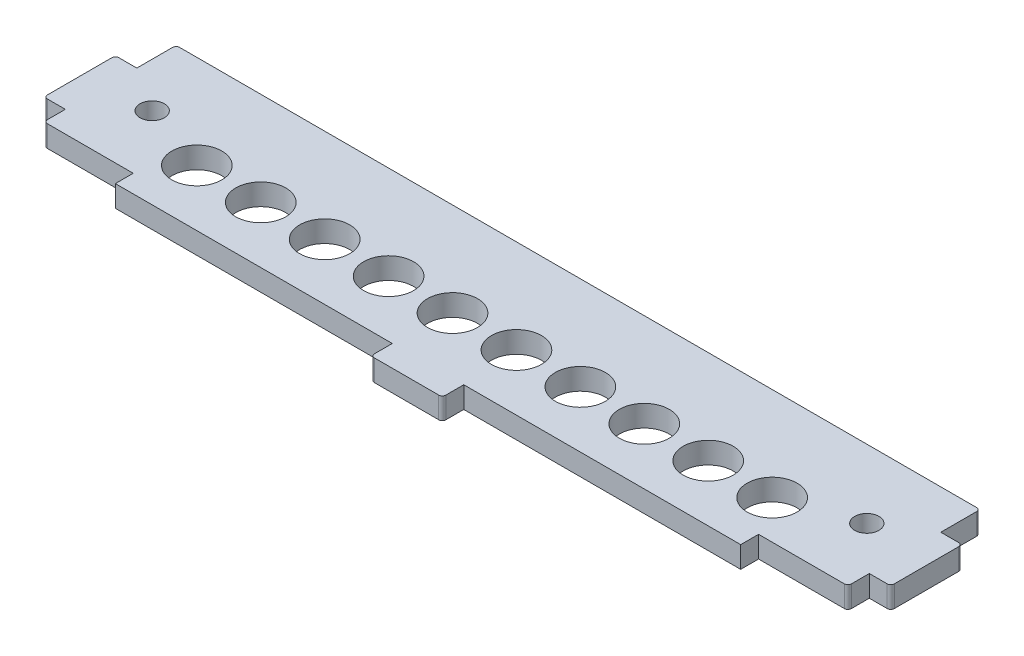
SolidWorks part; units mm, degrees
ref_plane "Спереди" through (0, 0, 0) normal (0, 0, 1) x (1, 0, 0)
ref_plane "Сверху" through (0, 0, 0) normal (0, 1, 0) x (1, 0, 0)
ref_plane "Справа" through (0, 0, 0) normal (1, 0, 0) x (0, 0, -1)
sketch "Эскиз1" plane through (0, 0, 0) normal (0, 1, 0) x (1, 0, 0)
  line L0 (0, -21) -> (0, 21.8864) construction
  line L1 (-43.75, -21) -> (43.75, -21)
  line L2 (43.75, -21) -> (43.75, -18.5)
  line L3 (43.75, -18.5) -> (56.25, -18.5)
  line L4 (56.25, -18.5) -> (56.25, -15.5)
  line L5 (56.25, -15.5) -> (59.25, -15.5)
  line L6 (59.25, -15.5) -> (59.25, -5.5)
  line L7 (59.25, -5.5) -> (56.25, -5.5)
  line L8 (56.25, -5.5) -> (56.25, 0)
  line L9 (56.25, 0) -> (-56.25, 0)
  line L10 (-56.25, -5.5) -> (-56.25, 0)
  line L11 (-59.25, -5.5) -> (-56.25, -5.5)
  line L12 (-59.25, -15.5) -> (-59.25, -5.5)
  line L13 (-56.25, -15.5) -> (-59.25, -15.5)
  line L14 (-56.25, -18.5) -> (-56.25, -15.5)
  line L15 (-43.75, -18.5) -> (-56.25, -18.5)
  line L16 (-43.75, -21) -> (-43.75, -18.5)
  line L17 (52.2732, -10.5) -> (61.8348, -10.5) construction
  line L18 (-50, -9.6) -> (-50, -5.5) construction
  line L19 (-5, -24) -> (5, -24)
  line L20 (-5, -24) -> (-5, -21)
  line L21 (-5, -21) -> (5, -21)
  line L22 (5, -24) -> (5, -21)
  line L23 (-5, -24) -> (5, -21) construction
  line L24 (-5, -21) -> (5, -24) construction
  line L25 (50, -9.6) -> (50, -6.794) construction
  circle A0 centre (-40.25, -13.1) radius 3.5
  circle A1 centre (-31.3056, -13.1) radius 3.5
  circle A2 centre (-22.3611, -13.1) radius 3.5
  circle A3 centre (-13.4167, -13.1) radius 3.5
  circle A4 centre (-4.4722, -13.1) radius 3.5
  circle A5 centre (4.4722, -13.1) radius 3.5
  circle A6 centre (13.4167, -13.1) radius 3.5
  circle A7 centre (22.3611, -13.1) radius 3.5
  circle A8 centre (31.3056, -13.1) radius 3.5
  circle A9 centre (40.25, -13.1) radius 3.5
  point P14 (50, -9.6)
  point P18 (0, 0)
  point P25 (-50, -9.6)
  point P45 (0, -22.5)
  dimension "D10" = 7
  dimension "D15" = 10
  dimension "D1" = 3
  dimension "D2" = 10
  dimension "D3" = 12.5
  dimension "D4" = 21
  dimension "D5" = 18.5
  dimension "D6" = 10.5
  dimension "D7" = 100
  dimension "D8" = 6.25
  dimension "D9" = 9.6
  dimension "D12" = 6.25
  dimension "D13" = 6.25
  dimension "D14" = 3.5
  dimension "D16" = 3
  dimension "D11" = 10
extrude "Бобышка-Вытянуть1" add sketch "Эскиз1" along normal blind 3 contours L0 L1 L2 L3 L4 L5 L6 L7 L8 L9 A9 A8 A7 A6 A5 | L1 L0 L9 L10 L11 L12 L13 L14 L15 L16 A0 A1 A2 A3 A4 | L19 L22 L1 L20
hole_wizard "Отверстие с зазором M31" positions "Эскиз2" profile "Эскиз3" hole size "M3" standard "IS"
sketch "Эскиз2" plane through (0, 3, 0) normal (0, 1, 0) x (1, 0, 0)
  point P0 (50, -9.6)
  point P2 (-50, -9.6)
sketch "Эскиз3" plane through (50, 3, 9.6) normal (1, 0, 0) x (0, 0, 1)
  line L0 (0, 0) -> (0, 11.0215)
  line L1 (0, 11.0215) -> (1.7, 10)
  line L2 (1.7, 10) -> (1.7, 0)
  line L5 (1.7, 0) -> (0, 0)
  line L10 (0, 11.0215) -> (-1.7, 10) construction
  line L11 (0, -6.35) -> (0, 107.95) construction
  dimension "Диаметр отверстия" = 3.4
  dimension "Глубина отверстия" = 10
  dimension "Угол заточки сверла" = 118
sketch "Эскиз4" plane through (0, 3, 0) normal (0, 1, 0) x (1, 0, 0)
  line L0 (-22.3611, -17.3679) -> (-20.8611, -19.966)
  line L1 (-42.25, -18.35) -> (-38.25, -18.35)
  line L2 (-42.25, -18.35) -> (-42.25, -19.85)
  line L3 (-42.25, -19.85) -> (-38.25, -19.85)
  line L4 (-38.25, -18.35) -> (-38.25, -19.85)
  line L5 (-42.25, -18.35) -> (-38.25, -19.85) construction
  line L6 (-42.25, -19.85) -> (-38.25, -18.35) construction
  line L7 (-20.8611, -19.966) -> (-23.8611, -19.966)
  line L8 (-23.8611, -19.966) -> (-22.3611, -17.3679)
  line L9 (-15.9167, -19.85) -> (-10.9167, -19.85)
  line L10 (-23.8611, -19.966) -> (-21.6111, -18.667) construction
  line L11 (-5.9722, -20.6) -> (-2.9722, -20.6)
  line L12 (-5.9722, -20.6) -> (-5.9722, -17.6)
  line L13 (-5.9722, -17.6) -> (-2.9722, -17.6)
  line L14 (-2.9722, -20.6) -> (-2.9722, -17.6)
  line L15 (-22.3611, -17.3679) -> (-22.3611, -19.1) construction
  line L16 (-13.4167, -19.85) -> (-13.4167, -18.35) construction
  line L17 (-5.9722, -20.6) -> (-2.9722, -17.6) construction
  line L18 (-5.9722, -17.6) -> (-2.9722, -20.6) construction
  circle A0 centre (-31.3056, -19.1) radius 1.5
  arc A1 (-15.9167, -19.85) -> (-10.9167, -19.85) centre (-13.4167, -21.1833) cw
  point P0 (-40.25, -19.1)
  point P20 (-4.4722, -17.6)
  point P22 (-13.4167, -19.85)
  point P24 (-22.3611, -19.966)
  point P33 (-13.4167, -19.1)
  point P34 (-4.4722, -19.1)
  dimension "D3" = 3
  dimension "D5" = 1.5
  dimension "D1" = 3
  dimension "D2" = 1.5
  dimension "D4" = 3
  dimension "D6" = 6
  dimension "D7" = 4
  dimension "D8" = 5
extrude "Вырез-Вытянуть1" [suppressed] cut sketch "Эскиз4" against normal blind 0.3
fillet "Скругление1" radius 0.5 4 edges at (-59.25, 1.5, 5.5) (-59.25, 1.5, 15.5) (59.25, 1.5, 5.5) (59.25, 1.5, 15.5)
fillet "Скругление2" radius 0.5 6 edges at (-56.25, 1.5, 0) (-56.25, 1.5, 18.5) (56.25, 1.5, 0) (56.25, 1.5, 18.5) (-5, 1.5, 24) (5, 1.5, 24)
